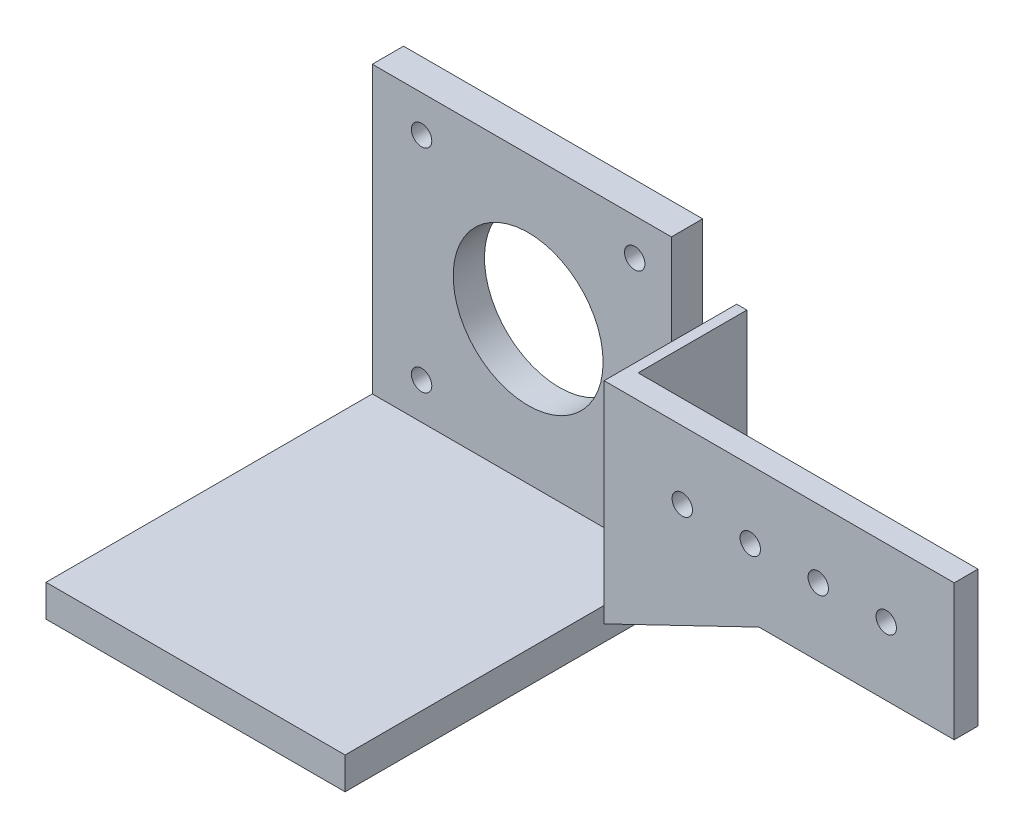
SolidWorks part; units mm, degrees
ref_plane "Ön Düzlem" through (0, 0, 0) normal (0, 0, 1) x (1, 0, 0)
ref_plane "Üst Düzlem" through (0, 0, 0) normal (0, 1, 0) x (1, 0, 0)
ref_plane "Sağ Düzlem" through (0, 0, 0) normal (1, 0, 0) x (0, 0, -1)
sketch "Çizim1" plane through (0, 0, 0) normal (0, 0, 1) x (1, 0, 0)
  line L1 (-25, 10) -> (25, 10)
  line L2 (-25, 10) -> (-25, -10)
  line L3 (-25, -10) -> (25, -10)
  line L4 (25, 10) -> (25, -10)
  line L5 (-25, 10) -> (25, -10) construction
  line L6 (-25, -10) -> (25, 10) construction
  circle A0 centre (-15, 0) radius 1.5
  circle A1 centre (-5, 0) radius 1.5
  circle A2 centre (5, 0) radius 1.5
  circle A3 centre (15, 0) radius 1.5
  point P0 (0, 0)
  dimension "D3" = 3
  dimension "D4" = 3
  dimension "D5" = 3
  dimension "D6" = 3
  dimension "D7" = 10
  dimension "D8" = 10
  dimension "D9" = 10
  dimension "D10" = 10
  dimension "D1" = 50
  dimension "D2" = 20
extrude "Yükseklik-Ekstrüzyon1" add sketch "Çizim1" along normal blind 3.5
sketch "Çizim2" plane through (-25, 0, 0) normal (-1, 0, 0) x (0, 0, 1)
  line L5 (3.5, 10) -> (-16, 10)
  line L6 (3.5, 10) -> (3.5, -9.9628)
  line L7 (3.5, -9.9628) -> (-16, -9.9628)
  line L8 (-16, 10) -> (-16, -9.9628)
  circle A0 centre (-8.8, 0.4964) radius 2
  dimension "D2" = 12.3
  dimension "D3" = 4
  dimension "D1" = 19.5
extrude "Yükseklik-Ekstrüzyon2" add sketch "Çizim2" along normal blind 1.5
sketch "Çizim4" plane through (-26.5, 0, 0) normal (-1, 0, 0) x (0, 0, 1)
  circle A0 centre (-8.8, 0.4964) radius 3
  dimension "D1" = 6
extrude "Kes-Ekstrüzyon1" cut sketch "Çizim4" against normal blind 0.5
sketch "Çizim5" plane through (-26.5, 0, 0) normal (-1, 0, 0) x (0, 0, 1)
  line L0 (-16, 10) -> (-16, -9.9628) construction
  line L1 (-11, 23.37) -> (-6.4, 23.37)
  line L2 (-11, 23.37) -> (-11, -23.33)
  line L3 (-11, -23.33) -> (-6.4, -23.33)
  line L4 (-6.4, 23.37) -> (-6.4, -23.33)
  line L6 (3.5, 10) -> (-16, 10) construction
  dimension "D1" = 46.7
  dimension "5" = 5
  dimension "D2" = 4.6
  dimension "D3" = 13.37
extrude "Yükseklik-Ekstrüzyon3" add sketch "Çizim5" along normal blind 52
sketch "Çizim6" plane through (0, 0, -6.4) normal (0, 0, 1) x (1, 0, 0)
  line L0 (-26.5, -23.33) -> (-26.5, -9.9628) construction
  line L1 (-78.5, -23.33) -> (-26.5, -23.33)
  line L2 (-78.5, -23.33) -> (-78.5, -18.63)
  line L3 (-78.5, -18.63) -> (-26.5, -18.63)
  line L4 (-26.5, -23.33) -> (-26.5, -18.63)
  dimension "D1" = 4.7
extrude "Yükseklik-Ekstrüzyon4" add sketch "Çizim6" along normal blind 48
sketch "Çizim7" plane through (-25, 0, 0) normal (1, 0, 0) x (0, 0, -1)
  circle A0 centre (8.8, 0.4964) radius 2
extrude "Yükseklik-Ekstrüzyon7" add sketch "Çizim7" against normal up to surface (1 mm away) up to face at (-26, 0.4964, -6.8)
sketch "Çizim8" plane through (0, 0, -6.4) normal (0, 0, 1) x (1, 0, 0)
  line L5 (-47.575, 23.37) -> (-47.575, -6.6299) construction
  line L6 (-68.65, 2.37) -> (-60.4108, 2.37) construction
  circle A0 centre (-31.9, -13.23) radius 1.5
  circle A1 centre (-63.25, -13.23) radius 1.5
  circle A2 centre (-31.9, 17.97) radius 1.5
  circle A3 centre (-63.25, 17.97) radius 1.5
  circle A4 centre (-47.575, 2.37) radius 11.025
  dimension "D3" = 3
  dimension "D6" = 22.05
extrude "Kes-Ekstrüzyon3" cut sketch "Çizim8" against normal blind 67
sketch "Çizim9" plane through (0, 0, -6.4) normal (0, 0, 1) x (1, 0, 0)
  line L1 (-78.5, 23.37) -> (-70.5, 23.37)
  line L2 (-78.5, 23.37) -> (-78.5, -29.2122)
  line L3 (-78.5, -29.2122) -> (-70.5, -29.2122)
  line L4 (-70.5, 23.37) -> (-70.5, -29.2122)
  dimension "D1" = 8
extrude "Kes-Ekstrüzyon4" cut sketch "Çizim9" along normal blind 86
sketch "Çizim10" plane through (0, 0, -6.4) normal (0, 0, 1) x (1, 0, 0)
  line L1 (-78.5, 23.37) -> (-70.5, 23.37)
  line L2 (-78.5, 23.37) -> (-78.5, -30.7126)
  line L3 (-78.5, -30.7126) -> (-70.5, -30.7126)
  line L4 (-70.5, 23.37) -> (-70.5, -30.7126)
  dimension "D1" = 8
extrude "Kes-Ekstrüzyon5" cut sketch "Çizim10" against normal blind 86
sketch "Çizim12" plane through (0, 0, 3.5) normal (0, 0, 1) x (1, 0, 0)
  line L0 (-26.5, -20.98) -> (-26.5, -5.6332)
  line L1 (-26.5, -23.33) -> (-26.5, -18.63) construction
  line L2 (-26.5, -9.9628) -> (-26.5, -1.3036) construction
  line L3 (-26.5, -5.6332) -> (5.3485, -5.6332)
  line L4 (5.3485, -5.6332) -> (-26.5, -20.98)
extrude "Yükseklik-Ekstrüzyon13" add sketch "Çizim12" against normal up to surface (3.5 mm away) up to face at (-5, -1.9926, 0)
sketch "Çizim13" plane through (-26.5, 0, 0) normal (1, 0, 0) x (0, 0, -1)
  line L0 (0, -20.98) -> (0, -9.9628)
  line L1 (0, -9.9628) -> (11, -9.9628)
  line L2 (11, -9.9628) -> (11, -20.98)
  line L3 (11, -9.9628) -> (11, -23.33) construction
  line L4 (11, -20.98) -> (0, -20.98)
extrude "Yükseklik-Ekstrüzyon15" add sketch "Çizim13" along normal up to surface (1.5 mm away) up to face at (-25, 0.0186, -8)
